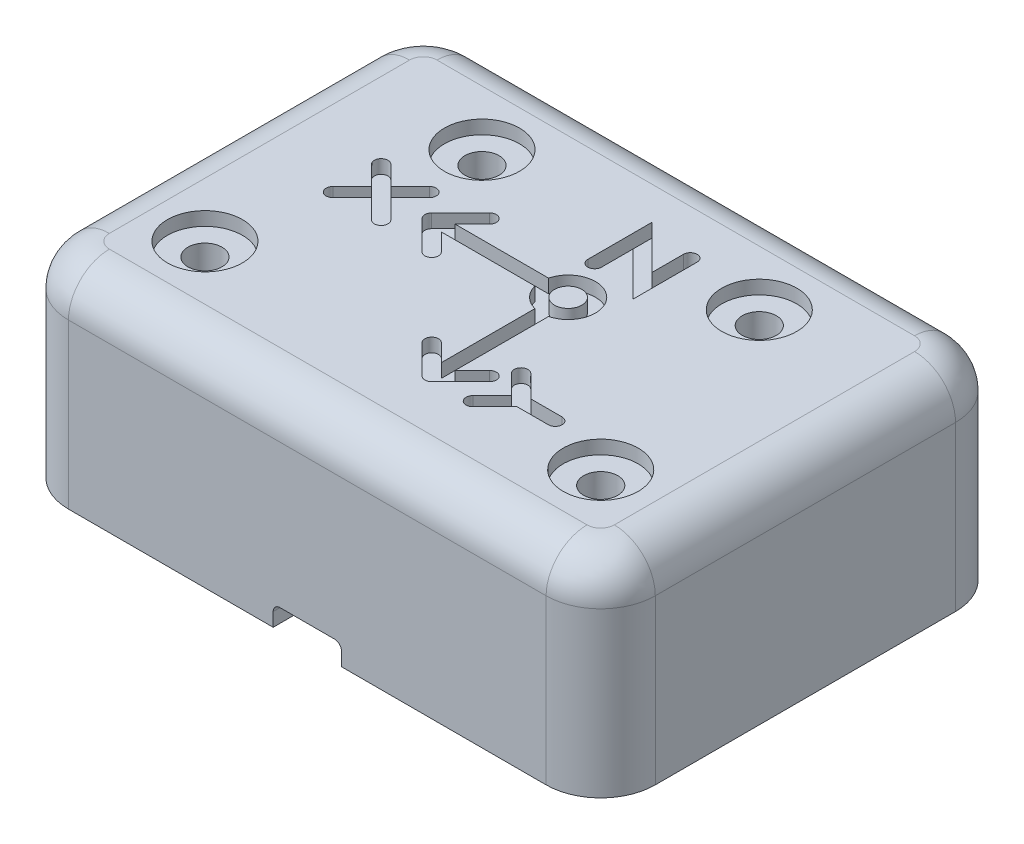
SolidWorks part; units mm, degrees
ref_plane "Front Plane" through (0, 0, 0) normal (0, 0, 1) x (1, 0, 0)
ref_plane "Top Plane" through (0, 0, 0) normal (0, 1, 0) x (1, 0, 0)
ref_plane "Right Plane" through (0, 0, 0) normal (1, 0, 0) x (0, 0, -1)
sketch "Sketch1" plane through (0, 0, 0) normal (0, 1, 0) x (1, 0, 0)
  line L1 (4, 0) -> (39, 0)
  line L2 (0, 4) -> (0, 26)
  line L3 (4, 30) -> (39, 30)
  line L4 (43, 4) -> (43, 26)
  arc A0 (39, 30) -> (43, 26) centre (39, 26) cw
  arc A1 (39, 0) -> (43, 4) centre (39, 4) ccw
  arc A2 (4, 0) -> (0, 4) centre (4, 4) cw
  arc A3 (0, 26) -> (4, 30) centre (4, 26) cw
  point P7 (43, 30)
  point P10 (43, 0)
  point P13 (0, 0)
  point P16 (0, 30)
  dimension "D3" = 4
  dimension "D1" = 43
  dimension "D2" = 30
extrude "Boss-Extrude1" add sketch "Sketch1" along normal blind 15
sketch "Sketch2" plane through (0, 0, 0) normal (0, -1, 0) x (1, 0, 0)
  line L0 (4, 0) -> (39, 0) construction
  line L1 (4, -2) -> (39, -2)
  line L2 (2, -4) -> (2, -26)
  line L3 (4, -28) -> (39, -28)
  line L4 (41, -4) -> (41, -26)
  line L5 (43, -4) -> (43, -26) construction
  line L6 (39, -30) -> (4, -30) construction
  line L7 (0, -26) -> (0, -4) construction
  arc A0 (39, -28) -> (41, -26) centre (39, -26) ccw
  arc A1 (2, -26) -> (4, -28) centre (4, -26) ccw
  arc A2 (39, -2) -> (41, -4) centre (39, -4) cw
  arc A3 (4, -2) -> (2, -4) centre (4, -4) ccw
  dimension "D5" = 2
  dimension "D1" = 2
  dimension "D2" = 2
  dimension "D3" = 2
  dimension "D4" = 2
extrude "Cut-Extrude1" cut sketch "Sketch2" against normal blind 12
fillet "Fillet1" radius 3 8 edges at (41.8284, 15, -1.1716) (21.5, 15, 0) (1.1716, 15, -1.1716) (0, 15, -15) (1.1716, 15, -28.8284) (21.5, 15, -30) (41.8284, 15, -28.8284) (43, 15, -15)
fillet "Fillet2" radius 1.5 8 edges at (40.4142, 12, -27.4142) (21.5, 12, -28) (2.5858, 12, -27.4142) (2, 12, -15) (2.5858, 12, -2.5858) (21.5, 12, -2) (40.4142, 12, -2.5858) (41, 12, -15)
sketch "Sketch6" plane through (0, 15, 0) normal (0, 1, 0) x (1, 0, 0)
  line L1 (23.365, 14.8145) -> (23.365, 7.9581)
  line L2 (24.365, 14.8145) -> (24.365, 7.9581)
  line L3 (11.0419, 16.578) -> (12.4561, 17.9922)
  line L4 (21.9285, 16.251) -> (15.0721, 16.251)
  line L8 (13.5115, 16.3975) -> (15.6328, 14.2761)
  line L9 (15.0721, 17.251) -> (16.3399, 18.5188)
  line L10 (23.365, 7.9581) -> (22.0973, 9.2259)
  line L11 (24.2186, 6.3975) -> (26.3399, 8.5188)
  line L14 (15.0721, 16.251) -> (16.3399, 14.9833)
  line L15 (13.5115, 17.1046) -> (15.6328, 19.2259)
  line L16 (23.5115, 6.3975) -> (21.3902, 8.5188)
  line L17 (24.365, 7.9581) -> (25.6328, 9.2259)
  line L18 (21.9285, 17.251) -> (15.0721, 17.251)
  line L24 (8.9206, 14.4567) -> (10.3348, 15.8709)
  line L25 (8.2135, 17.9922) -> (9.6277, 16.578)
  line L26 (27.3192, 6.314) -> (28.9405, 7.9353)
  line L27 (28.9405, 8.9353) -> (27.3192, 10.5566)
  line L28 (28.9405, 7.9353) -> (31.2334, 7.9353)
  line L29 (23.177, 19.8837) -> (23.177, 22.1766)
  line L30 (23.177, 22.1766) -> (26.3589, 18.9946)
  line L31 (26.3589, 18.9946) -> (26.3589, 23.7054)
  line L32 (8.2135, 15.1638) -> (9.6277, 16.578)
  line L33 (8.9206, 18.6993) -> (10.3348, 17.2851)
  line L34 (26.612, 7.0211) -> (28.0263, 8.4353)
  line L35 (28.0263, 8.4353) -> (26.612, 9.8495)
  line L36 (28.9405, 8.9353) -> (31.2334, 8.9353)
  line L37 (22.177, 19.8837) -> (22.177, 24.5908)
  line L38 (22.177, 24.5908) -> (25.3589, 21.4088)
  line L39 (25.3589, 21.4088) -> (25.3589, 23.7054)
  line L41 (10.3348, 15.8709) -> (11.749, 14.4567)
  line L45 (11.0419, 16.578) -> (12.4561, 15.1638)
  line L47 (10.3348, 17.2851) -> (11.749, 18.6993)
  arc A1 (21.9285, 16.251) -> (23.365, 14.8145) centre (23.865, 16.751) ccw
  circle A2 centre (23.865, 16.751) radius 1
  arc A3 (24.2186, 6.3975) -> (23.5115, 6.3975) centre (23.865, 6.751) cw
  arc A4 (13.5115, 17.1046) -> (13.5115, 16.3975) centre (13.865, 16.751) ccw
  arc A5 (13.5115, 16.3975) -> (13.5115, 17.1046) centre (13.865, 16.751) cw
  arc A6 (15.6328, 14.2761) -> (16.3399, 14.9833) centre (15.9864, 14.6297) ccw
  arc A7 (13.5115, 16.3975) -> (13.5115, 17.1046) centre (13.865, 16.751) cw
  arc A8 (16.3399, 18.5188) -> (15.6328, 19.2259) centre (15.9864, 18.8723) ccw
  arc A9 (24.2186, 6.3975) -> (23.5115, 6.3975) centre (23.865, 6.751) cw
  arc A10 (22.0973, 9.2259) -> (21.3902, 8.5188) centre (21.7437, 8.8723) ccw
  arc A11 (24.2186, 6.3975) -> (23.5115, 6.3975) centre (23.865, 6.751) cw
  arc A12 (26.3399, 8.5188) -> (25.6328, 9.2259) centre (25.9864, 8.8723) ccw
  arc A13 (8.9206, 14.4567) -> (8.2135, 15.1638) centre (8.567, 14.8103) cw
  arc A14 (24.365, 14.8145) -> (21.9285, 17.251) centre (23.865, 16.751) ccw
  arc A15 (12.4561, 17.9922) -> (11.749, 18.6993) centre (12.1026, 18.3458) ccw
  arc A16 (8.2135, 17.9922) -> (8.9206, 18.6993) centre (8.567, 18.3458) cw
  arc A17 (11.749, 14.4567) -> (12.4561, 15.1638) centre (12.1026, 14.8103) ccw
  arc A18 (27.3192, 6.314) -> (26.612, 7.0211) centre (26.9656, 6.6675) cw
  arc A21 (27.3192, 10.5566) -> (26.612, 9.8495) centre (26.9656, 10.2031) ccw
  arc A23 (31.2334, 7.9353) -> (31.2334, 8.9353) centre (31.2334, 8.4353) ccw
  arc A24 (23.177, 19.8837) -> (22.177, 19.8837) centre (22.677, 19.8837) cw
  arc A25 (26.3589, 23.7054) -> (25.3589, 23.7054) centre (25.8589, 23.7054) ccw
extrude "Cut-Extrude5" cut sketch "Sketch6" against normal blind 1 contours L2 A14 L18 L9 A8 L15 A4 L8 A6 L14 L4 A1 L1 L10 A10 L16 A3 L11 A12 L17 A2 | L31 A25 L39 L38 L37 A24 L29 L30 | L28 A23 L36 L27 A21 L35 L34 A18 L26 | L41 A17 L45 L3 A15 L47 L33 A16 L25 L32 A13 L24
sketch "Sketch7" plane through (0, 0, 0) normal (0, 0, 1) x (1, 0, 0)
  line L0 (4, 0) -> (39, 0) construction
  line L1 (19, 0) -> (24, 0)
  line L2 (19, 0) -> (19, 1)
  line L3 (19.5, 1.5) -> (23.5, 1.5)
  line L4 (24, 0) -> (24, 1)
  line L6 (4, 12) -> (4, 0) construction
  arc A0 (23.5, 1.5) -> (24, 1) centre (23.5, 1) cw
  arc A1 (19.5, 1.5) -> (19, 1) centre (19.5, 1) ccw
  point P10 (24, 1.5)
  point P13 (19, 1.5)
  dimension "D4" = 0.5
  dimension "D1" = 5
  dimension "D2" = 1.5
  dimension "D3" = 15
extrude "Cut-Extrude6" cut sketch "Sketch7" against normal blind 2 contours L3 A0 L4 L1 L2 A1
sketch "Sketch9" plane through (0, 15, 0) normal (0, 1, 0) x (1, 0, 0)
  line L0 (21.5, 3) -> (21.5, 27) construction
  line L1 (8.8, 10.26) -> (34.2, 10.26) construction
  line L2 (8.8, 10.26) -> (8.8, 25.5) construction
  line L3 (8.8, 25.5) -> (34.2, 25.5) construction
  line L4 (34.2, 10.26) -> (34.2, 25.5) construction
  line L5 (4, 3) -> (39, 3) construction
  line L6 (39, 27) -> (4, 27) construction
  line L7 (0, 4) -> (0, 26) construction
  line L8 (39, 0) -> (4, 0) construction
  line L9 (4, 30) -> (39, 30) construction
  circle A0 centre (7, 7) radius 1.25
  circle A1 centre (11.34, 22.96) radius 1.25
  circle A2 centre (31.66, 22.96) radius 1.25
  circle A3 centre (36, 7) radius 1.25
  dimension "D5" = 2.5
  dimension "D8" = 2.5
  dimension "D9" = 2.54
  dimension "D10" = 2.54
  dimension "D4" = 7
  dimension "D7" = 7
  dimension "D1" = 15.24
  dimension "D2" = 25.4
  dimension "D3" = 12.7
  dimension "D6" = 4.5
extrude "Cut-Extrude7" cut sketch "Sketch9" against normal blind 3
sketch "Sketch10" plane through (0, 15, 0) normal (0, 1, 0) x (1, 0, 0)
  circle A0 centre (7, 7) radius 2.75
  circle A1 centre (11.34, 22.96) radius 2.75
  circle A2 centre (36, 7) radius 2.75
  circle A3 centre (31.66, 22.96) radius 2.75
  dimension "D1" = 5.5
  dimension "D2" = 5.5
  dimension "D3" = 5.5
  dimension "D4" = 5.5
extrude "Cut-Extrude8" cut sketch "Sketch10" against normal blind 1
